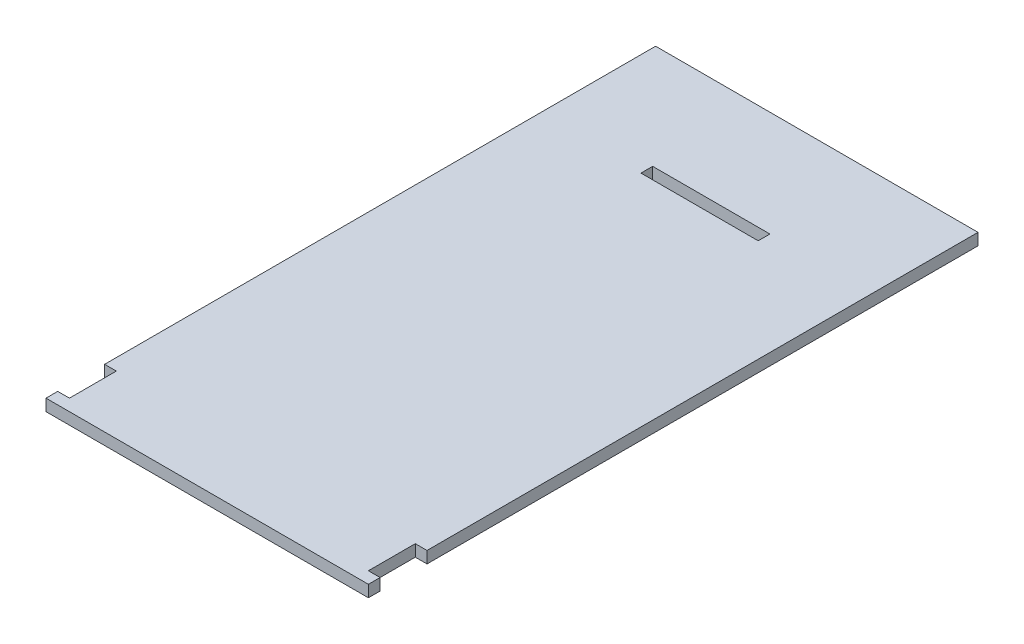
SolidWorks part; units mm, degrees
ref_plane "Front Plane" through (0, 0, 0) normal (0, 0, 1) x (1, 0, 0)
ref_plane "Top Plane" through (0, 0, 0) normal (0, 1, 0) x (1, 0, 0)
ref_plane "Right Plane" through (0, 0, 0) normal (1, 0, 0) x (0, 0, -1)
sketch "Sketch1" plane through (0, 0, 0) normal (0, 1, 0) x (1, 0, 0)
  line L0 (0, 2) -> (2, 2)
  line L1 (0, 0) -> (55, 0)
  line L3 (0, 104) -> (55, 104)
  line L5 (2, 2) -> (2, 10)
  line L6 (2, 10) -> (0, 10)
  line L7 (0, 0) -> (0, 2)
  line L8 (0, 10) -> (0, 104)
  line L9 (55, 0) -> (55, 2)
  line L10 (55, 2) -> (53, 2)
  line L11 (53, 2) -> (53, 10)
  line L12 (53, 10) -> (55, 10)
  line L13 (55, 10) -> (55, 104)
  line L14 (0, 84) -> (17.5, 84) construction
  line L15 (17.5, 86) -> (37.5, 86)
  line L16 (17.5, 86) -> (17.5, 84)
  line L17 (17.5, 84) -> (37.5, 84)
  line L18 (37.5, 86) -> (37.5, 84)
  line L19 (37.5, 84) -> (55, 84) construction
  dimension "D1" = 55
  dimension "D2" = 104
  dimension "D3" = 8
  dimension "D4" = 2
  dimension "D5" = 2
  dimension "D6" = 2
  dimension "D7" = 20
  dimension "D8" = 55
  dimension "D9" = 84
extrude "Boss-Extrude1" add sketch "Sketch1" along normal blind 2
